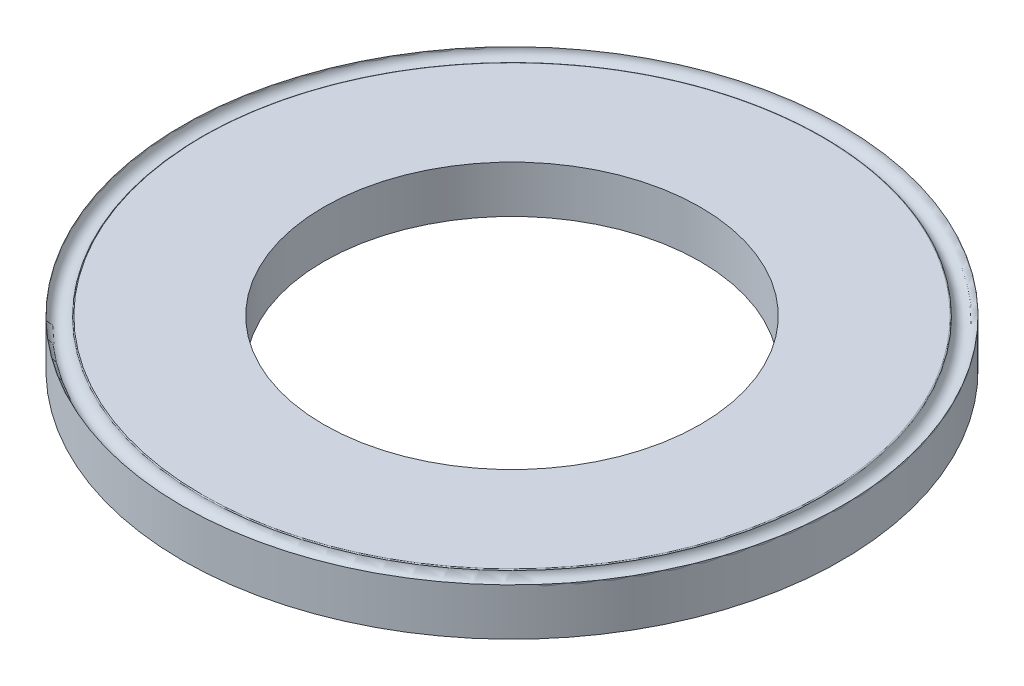
SolidWorks part; units mm, degrees
material "Chrome Stainless Steel"
ref_plane "Front Plane" through (0, 0, 0) normal (0, 0, 1) x (1, 0, 0)
ref_plane "Top Plane" through (0, 0, 0) normal (0, 1, 0) x (1, 0, 0)
ref_plane "Right Plane" through (0, 0, 0) normal (1, 0, 0) x (0, 0, -1)
sketch "DiaProfileS" plane through (0, 0, 0) normal (0, 1, 0) x (1, 0, 0)
  circle A0 centre (0, 0) radius 2
  circle A1 centre (0, 0) radius 3.5
  dimension "InnerDia" = 4
  dimension "Thickness" = 1.5
extrude "DiaProfile" add sketch "DiaProfileS" along normal mid plane 0.5
sketch "CrimpS" plane through (0, 0, 0) normal (0, 0, 1) x (1, 0, 0)
  line L0 (3.5, 0.25) -> (-3.5, 0.25) construction
  line L1 (-3.5, 0.25) -> (-3.5, -0.25) construction
  line L3 (-3.5, 0.25) -> (-3.2905, 0.25)
  arc A0 (-3.5, 0.25) -> (-3.3004, 0.2409) centre (-3.4, 0.25) ccw
  arc A2 (-3.3004, 0.2409) -> (-3.2905, 0.25) centre (-3.2905, 0.24) cw
  dimension "Dia" = 0.2
  dimension "Fillet" = 0.01
revolve "Crimp" cut sketch "CrimpS" angle 360 about axis through (0, 0.25, 0) along (0, -1, 0)
